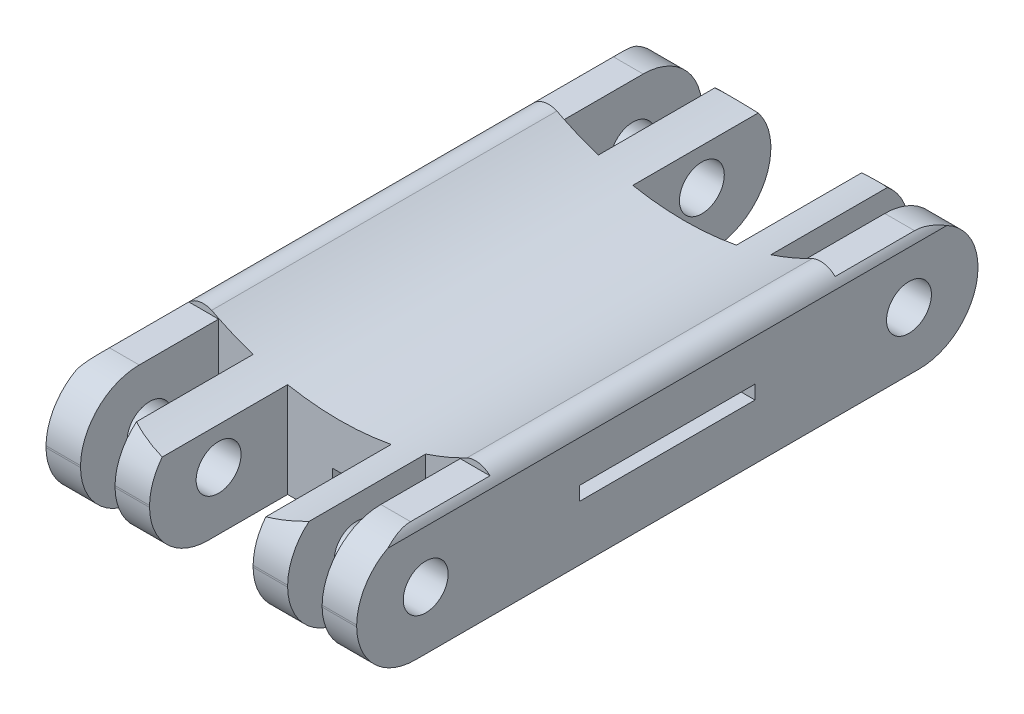
SolidWorks part; units mm, degrees
ref_plane "Front Plane" through (0, 0, 0) normal (0, 0, 1) x (1, 0, 0)
ref_plane "Top Plane" through (0, 0, 0) normal (0, 1, 0) x (1, 0, 0)
ref_plane "Right Plane" through (0, 0, 0) normal (1, 0, 0) x (0, 0, -1)
sketch "Sketch1" plane through (0, 0, 0) normal (0, 1, 0) x (1, 0, 0)
  line L0 (-22.5, 94) -> (-22.5, 74)
  line L1 (-22.5, 74) -> (-17.5, 74)
  line L2 (-17.5, 74) -> (-17.5, 94)
  line L3 (-12.5, 74) -> (-7.5, 74)
  line L4 (-17.5, 144) -> (-17.5, 164)
  line L6 (7.5, 74) -> (7.5, 94)
  line L7 (7.5, 74) -> (12.5, 74)
  line L8 (12.5, 74) -> (12.5, 94)
  line L9 (17.5, 74) -> (22.5, 74)
  line L10 (22.5, 74) -> (22.5, 94)
  line L11 (17.5, 94) -> (17.5, 74)
  line L12 (12.5, 74) -> (7.5, 74)
  line L13 (-17.5, 94) -> (-12.5, 94)
  line L14 (-7.5, 144) -> (-2.5, 144)
  line L17 (2.5, 144) -> (7.5, 144)
  line L18 (-7.5, 94) -> (-7.5, 74)
  line L19 (-12.5, 74) -> (-12.5, 94)
  line L20 (-12.5, 144) -> (-12.5, 164)
  line L21 (-12.5, 164) -> (-7.5, 164)
  line L22 (-7.5, 164) -> (-7.5, 144)
  line L23 (-17.5, 144) -> (-12.5, 144)
  line L27 (7.5, 144) -> (7.5, 164)
  line L28 (7.5, 164) -> (12.5, 164)
  line L29 (12.5, 164) -> (12.5, 144)
  line L30 (17.5, 144) -> (17.5, 164)
  line L31 (12.5, 144) -> (17.5, 144)
  line L32 (12.5, 94) -> (17.5, 94)
  line L33 (2.5, 94) -> (7.5, 94)
  line L34 (17.5, 164) -> (22.5, 164)
  line L35 (-7.5, 94) -> (-2.5, 94)
  line L36 (22.5, 164) -> (22.5, 144)
  line L37 (-2.5, 144) -> (2.5, 144)
  line L38 (-2.5, 94) -> (2.5, 94)
  line L40 (-22.5, 144) -> (-22.5, 164)
  line L42 (-22.5, 164) -> (-17.5, 164)
  line L48 (-22.5, 94) -> (-22.5, 144)
  line L66 (22.5, 144) -> (22.5, 94)
extrude "Boss-Extrude1" add sketch "Sketch1" along normal blind 20
sketch "Sketch2" plane through (0, 0, 50) normal (0, 0, 1) x (1, 0, 0)
  line L0 (-22.5, 20) -> (22.5, 20)
  line L1 (-22.5, 20) -> (-22.5, 16)
  line L2 (-22.5, 20) -> (-22.5, 0) construction
  line L4 (22.5, 20) -> (22.5, 0) construction
  line L5 (22.5, 16) -> (22.5, 20)
  arc A0 (-18.5, 17.6071) -> (18.5, 17.6071) centre (0, 53.0719) ccw
  arc A1 (-22.5, 16) -> (-18.5, 17.6071) centre (-19.6964, 14.8036) cw
  arc A2 (18.5, 17.6071) -> (22.5, 16) centre (19.6964, 14.8036) cw
sketch "Sketch7" plane through (22.5, 0, 0) normal (1, 0, 0) x (0, 0, -1)
  line L0 (82.4991, 17) -> (93.9991, 17)
  line L1 (73.9991, 20) -> (73.9991, 0)
  line L2 (155.4991, 0) -> (163.9991, 0)
  line L3 (82.4991, 20) -> (73.9991, 20)
  line L4 (155.4991, 17) -> (143.9991, 17)
  line L5 (73.9991, 0) -> (73.9991, 17)
  line L6 (82.4991, 0) -> (73.9991, 0)
  line L8 (155.4991, 20) -> (163.9991, 20)
  line L14 (93.9991, 17) -> (93.9991, 20)
  line L15 (93.9991, 20) -> (82.4991, 20)
  line L16 (143.9991, 17) -> (143.9991, 20)
  line L17 (143.9991, 20) -> (155.4991, 20)
  line L22 (163.9991, 20) -> (164.814, 20)
  line L23 (164.814, 20) -> (164.814, 0)
  line L24 (164.814, 0) -> (163.9991, 0)
  arc A0 (82.4991, 0) -> (82.4991, 17) centre (82.4991, 8.5) cw
  arc A1 (155.4991, 0) -> (155.4991, 17) centre (155.4991, 8.5) ccw
extrude "Cut-Extrude21" cut sketch "Sketch7" against normal blind 45
extrude "Cut-Extrude23" cut sketch "Sketch2" against normal blind 444
sketch "Sketch9" plane through (22.5, 0, 0) normal (1, 0, 0) x (0, 0, -1)
  circle A4 centre (153.9996, 8.466) radius 3.25
  circle A5 centre (84, 8.4051) radius 3.25
  circle A6 centre (178, 8.5) radius 3.15
  circle A7 centre (60, 8.5) radius 3.15
extrude "Cut-Extrude24" cut sketch "Sketch9" against normal blind 45
sketch "Sketch12" plane through (0, 0, 50) normal (0, 0, 1) x (1, 0, 0)
  line L0 (-1, 3.35) -> (-1, 6.55)
  line L3 (1, 3.35) -> (-1, 3.35)
  line L4 (1, 6.55) -> (1, 3.35)
  line L5 (0, 6.55) -> (1, 6.55)
  line L6 (0, 6.55) -> (-1, 6.55)
extrude "Cut-Extrude26" cut sketch "Sketch12" against normal blind 444
sketch "Sketch13" plane through (22.5, 0, 0) normal (1, 0, 0) x (0, 0, -1)
  line L2 (118.9991, 8) -> (131.6991, 8)
  line L3 (118.9991, 8) -> (106.2991, 8)
  line L4 (106.2991, 8) -> (106.2991, 10)
  line L5 (106.2991, 10) -> (131.6991, 10)
  line L6 (131.6991, 10) -> (131.6991, 8)
extrude "Cut-Extrude27" cut sketch "Sketch13" against normal blind 45
